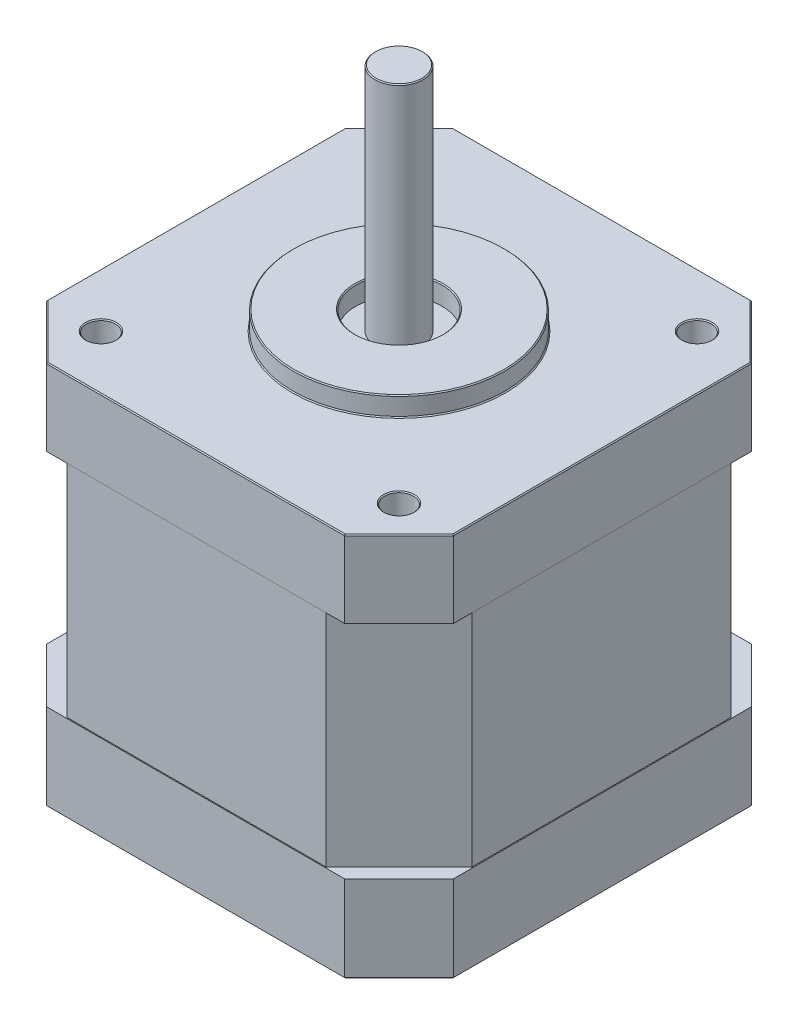
SolidWorks part; units mm, degrees
ref_plane "Front Plane" through (0, 0, 0) normal (0, 0, 1) x (1, 0, 0)
ref_plane "Top Plane" through (0, 0, 0) normal (0, 1, 0) x (1, 0, 0)
ref_plane "Right Plane" through (0, 0, 0) normal (1, 0, 0) x (0, 0, -1)
sketch "Sketch1" plane through (0, 0, 0) normal (0, 1, 0) x (1, 0, 0)
  line L0 (0, 0) -> (-12.9419, 0) construction
  line L1 (-15.5, -21.15) -> (15.5, -21.15)
  line L2 (-21.15, -15.5) -> (-21.15, 15.5)
  line L3 (-15.5, 21.15) -> (15.5, 21.15)
  line L4 (21.15, -15.5) -> (21.15, 15.5)
  line L5 (-21.15, -21.15) -> (21.15, 21.15) construction
  line L6 (-21.15, 21.15) -> (21.15, -21.15) construction
  line L7 (-21.15, 15.5) -> (-15.5, 21.15)
  line L8 (15.5, 21.15) -> (21.15, 15.5)
  line L9 (15.5, -21.15) -> (21.15, -15.5)
  line L10 (-21.15, -15.5) -> (-15.5, -21.15)
  circle A0 centre (-15.5, 15.5) radius 1.5
  circle A1 centre (15.5, -15.5) radius 1.5
  circle A2 centre (15.5, 15.5) radius 1.5
  circle A3 centre (-15.5, -15.5) radius 1.5
  point P0 (0, 0)
  dimension "D3" = 3
  dimension "D1" = 42.3
  dimension "D2" = 31
extrude "Boss-Extrude1" add sketch "Sketch1" along normal blind 9
sketch "Sketch4" plane through (0, 9, 0) normal (0, 1, 0) x (1, 0, 0)
  line L24 (13.4787, 21.05) -> (-13.4787, 21.05)
  line L25 (-21.05, 13.4787) -> (-21.05, -13.4787)
  line L26 (-13.4787, -21.05) -> (13.4787, -21.05)
  line L27 (21.05, -13.4787) -> (21.05, 13.4787)
  line L28 (-21.05, 13.4787) -> (-13.4787, 21.05)
  line L29 (-15.5, 21.15) -> (-21.15, 15.5) construction
  line L30 (13.4787, 21.05) -> (21.05, 13.4787)
  line L31 (21.05, -13.4787) -> (13.4787, -21.05)
  line L32 (-13.4787, -21.05) -> (-21.05, -13.4787)
  circle A0 centre (-15.5, 15.5) radius 1.5 construction
  circle A1 centre (15.5, 15.5) radius 1.5 construction
  circle A2 centre (15.5, -15.5) radius 1.5 construction
  circle A3 centre (-15.5, -15.5) radius 1.5 construction
  circle A4 centre (-15.5, 15.5) radius 1.5
  circle A5 centre (15.5, 15.5) radius 1.5
  circle A6 centre (15.5, -15.5) radius 1.5
  circle A7 centre (-15.5, -15.5) radius 1.5
  point P41 (0, 0)
  dimension "D2" = 1.5
  dimension "D3" = 4
extrude "Boss-Extrude4" add sketch "Sketch4" along normal blind 23
sketch "Sketch5" plane through (0, 32, 0) normal (0, 1, 0) x (1, 0, 0)
  line L9 (-15.5, 21.15) -> (-21.15, 15.5)
  line L10 (-21.15, 15.5) -> (-21.15, -15.5)
  line L11 (-21.15, -15.5) -> (-15.5, -21.15)
  line L12 (-15.5, -21.15) -> (15.5, -21.15)
  line L13 (15.5, -21.15) -> (21.15, -15.5)
  line L14 (21.15, -15.5) -> (21.15, 15.5)
  line L15 (21.15, 15.5) -> (15.5, 21.15)
  line L16 (15.5, 21.15) -> (-15.5, 21.15)
  line L17 (-15.5, 21.15) -> (-21.15, 15.5)
  line L18 (-21.15, 15.5) -> (-21.15, -15.5)
  line L19 (-21.15, -15.5) -> (-15.5, -21.15)
  line L20 (-15.5, -21.15) -> (15.5, -21.15)
  line L21 (15.5, -21.15) -> (21.15, -15.5)
  line L22 (21.15, -15.5) -> (21.15, 15.5)
  line L23 (21.15, 15.5) -> (15.5, 21.15)
  line L24 (15.5, 21.15) -> (-15.5, 21.15)
  circle A0 centre (15.5, 15.5) radius 1.5 construction
  circle A1 centre (-15.5, 15.5) radius 1.5 construction
  circle A2 centre (-15.5, -15.5) radius 1.5 construction
  circle A3 centre (15.5, -15.5) radius 1.5 construction
  circle A4 centre (15.5, 15.5) radius 1.5
  circle A5 centre (-15.5, 15.5) radius 1.5
  circle A6 centre (-15.5, -15.5) radius 1.5
  circle A7 centre (15.5, -15.5) radius 1.5
  dimension "D1" = 0
extrude "Boss-Extrude6" add sketch "Sketch5" along normal blind 8
sketch "Sketch2" plane through (0, 40, 0) normal (0, 1, 0) x (1, 0, 0)
  circle A0 centre (0, 0) radius 11
  circle A1 centre (0, 0) radius 4.5
  dimension "D1" = 22
  dimension "D2" = 9
extrude "Boss-Extrude2" add sketch "Sketch2" along normal blind 2
sketch "Sketch3" plane through (0, 40, 0) normal (0, 1, 0) x (1, 0, 0)
  circle A0 centre (0, 0) radius 2.5
  dimension "D1" = 5
extrude "Boss-Extrude3" add sketch "Sketch3" along normal offset from surface (24 mm away) 22 up to face at (0, 42, 11) offset beyond the face yes
chamfer "Chamfer1" distance 0.1 angle 45 28 edges at (-15.5, 0, 14) (15.5, 0, 14) (-21.15, 0, 0) (-18.325, 0, 18.325) (0, 0, 21.15) (18.325, 0, 18.325) (21.15, 0, 0) (18.325, 0, -18.325) (0, 0, -21.15) (-18.325, 0, -18.325) (-15.5, 0, -14) (15.5, 0, -14) (0, 40, 11) (15.5, 40, 17) (-15.5, 40, -14) (18.325, 40, -18.325) (21.15, 40, 0) (18.325, 40, 18.325) (0, 40, 21.15) (-18.325, 40, 18.325) (-21.15, 40, 0) (-18.325, 40, -18.325) (0, 40, -21.15) (15.5, 40, -14) (-15.5, 40, 17) (0, 64, 2.5) (0, 42, 4.5) (0, 42, 11)
